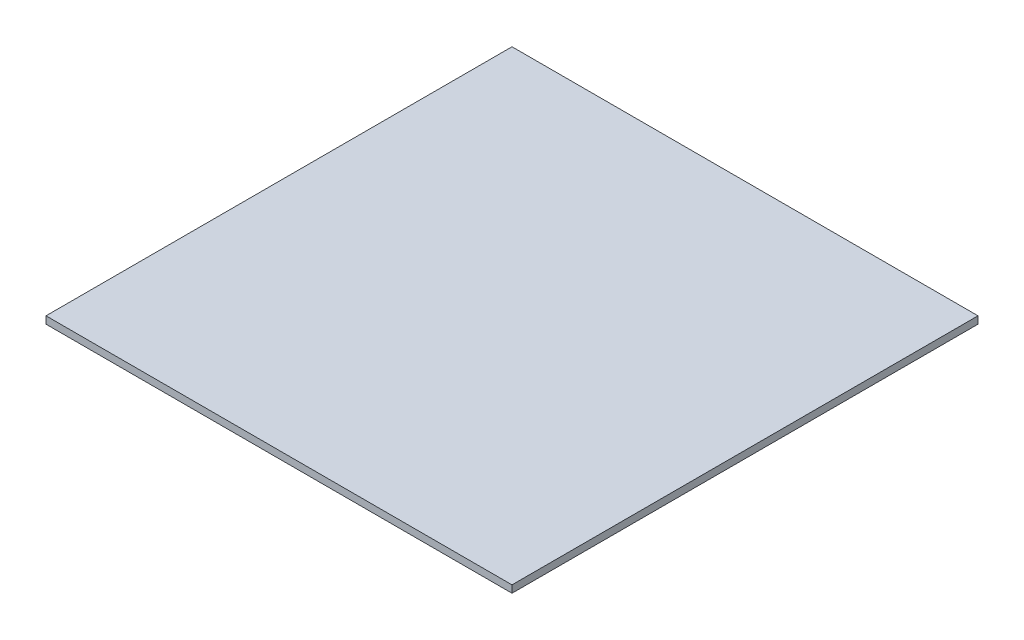
SolidWorks part; units mm, degrees
ref_plane "Front Plane" through (0, 0, 0) normal (0, 0, 1) x (1, 0, 0)
ref_plane "Top Plane" through (0, 0, 0) normal (0, 1, 0) x (1, 0, 0)
ref_plane "Right Plane" through (0, 0, 0) normal (1, 0, 0) x (0, 0, -1)
sketch "Sketch1" plane through (0, 0, 0) normal (0, 1, 0) x (1, 0, 0)
  line L1 (101.6, -101.6) -> (-101.6, -101.6)
  line L2 (101.6, -101.6) -> (101.6, 101.6)
  line L3 (101.6, 101.6) -> (-101.6, 101.6)
  line L4 (-101.6, -101.6) -> (-101.6, 101.6)
  line L5 (101.6, -101.6) -> (-101.6, 101.6) construction
  line L6 (101.6, 101.6) -> (-101.6, -101.6) construction
  point P0 (0, 0)
  dimension "D1" = 203.2
  dimension "D2" = 203.2
extrude "Boss-Extrude1" add sketch "Sketch1" along normal blind 3.175
